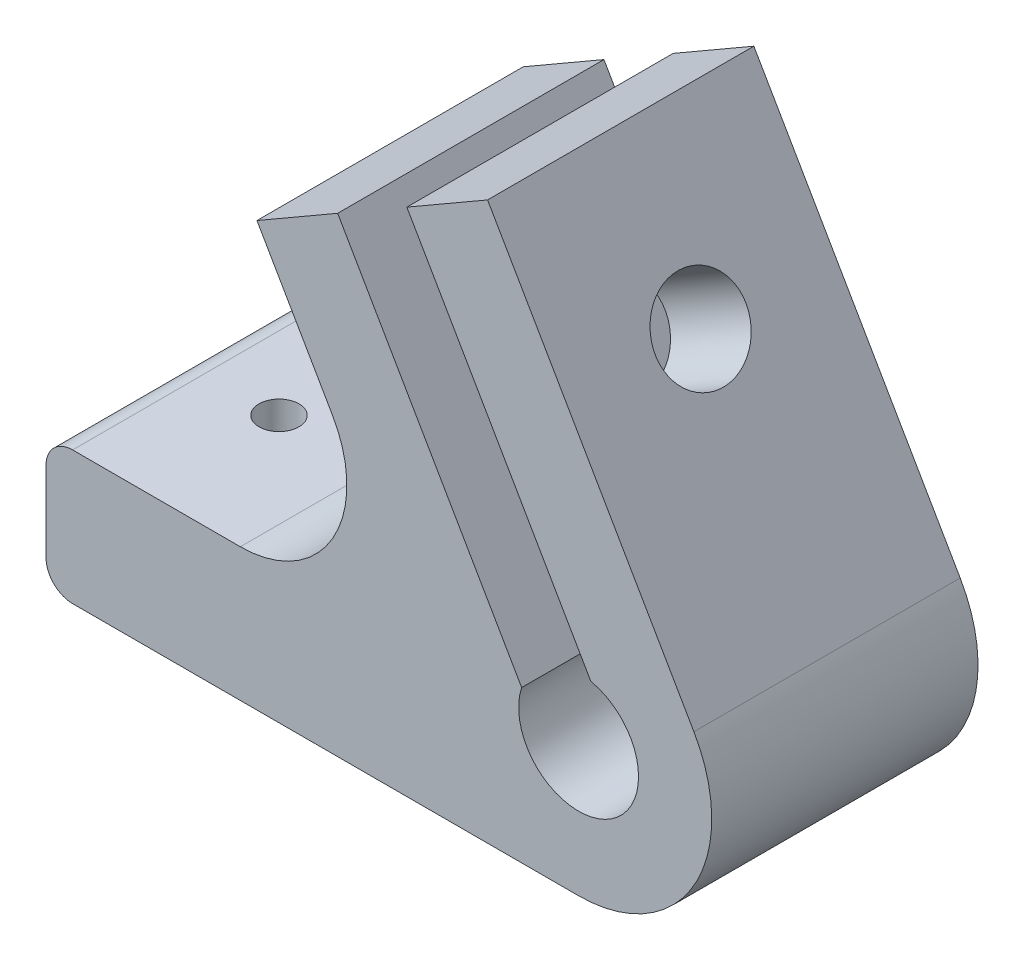
SolidWorks part; units mm, degrees
ref_plane "前视基准面" through (0, 0, 0) normal (0, 0, 1) x (1, 0, 0)
ref_plane "上视基准面" through (0, 0, 0) normal (0, 1, 0) x (1, 0, 0)
ref_plane "右视基准面" through (0, 0, 0) normal (1, 0, 0) x (0, 0, -1)
ref_plane "基准面4" through (0, 0, 10) normal (0, 0, 1) x (1, 0, 0)
sketch "草图1" plane through (0, 0, 10) normal (0, 0, 1) x (1, 0, 0)
  line L0 (904.3301, 2.5) -> (896.5815, 15.921)
  line L1 (896.5815, 15.921) -> (887.9212, 10.921)
  line L2 (887.9212, 10.921) -> (890.7624, 6)
  line L3 (887.2983, 0) -> (880, 0)
  line L4 (880, 0) -> (880, -5)
  line L5 (880, -5) -> (900, -5)
  arc A0 (890.7624, 6) -> (887.2983, 0) centre (887.2983, 4) cw
  arc A1 (900, -5) -> (904.3301, 2.5) centre (900, 0) ccw
extrude "凸台-拉伸1" add sketch "草图1" against normal blind 10
sketch "草图2" plane through (0, 0, 0) normal (0, 0, -1) x (-1, 0, 0)
  line L0 (-890.9523, 12.671) -> (-893.5504, 14.171)
  line L1 (-893.5504, 14.171) -> (-900.4605, 2.2024)
  line L2 (-897.8624, 0.7024) -> (-890.9523, 12.671)
  arc A0 (-900.4605, 2.2024) -> (-897.8624, 0.7024) centre (-900, 0) cw
extrude "切除-拉伸1" cut sketch "草图2" against normal through all
ref_plane "基准面5" through (671.5359, 387.7114, 0) normal (0.866, 0.5, 0) x (-0.5, 0.866, 0)
sketch "草图3" plane through (671.5359, 387.7114, 0) normal (0.866, 0.5, 0) x (-0.5, 0.866, 0)
  line L0 (-437.6448, 6.65) -> (-440.5027, 8.3)
  line L1 (-440.5027, 8.3) -> (-443.3606, 6.65)
  line L2 (-443.3606, 6.65) -> (-443.3606, 3.35)
  line L3 (-443.3606, 3.35) -> (-440.5027, 1.7)
  line L4 (-440.5027, 1.7) -> (-437.6448, 3.35)
  line L5 (-437.6448, 3.35) -> (-437.6448, 6.65)
extrude "切除-拉伸2" cut sketch "草图3" against normal up to next
sketch "草图4" plane through (0, 0, 0) normal (0, 1, 0) x (1, 0, 0)
  line L0 (902.25, 0) -> (900, 0)
  line L1 (900, 0) -> (900, -10)
  line L2 (900, -10) -> (902.25, -10)
  line L3 (902.25, -10) -> (902.25, 0)
  line L4 (900, 0) -> (900, -10) construction
revolve "切除-旋转1" cut sketch "草图4" angle 360 about L4
hole_wizard "Ø3.4 (3.4) 直径孔1" positions "草图6" profile "草图5" hole size "Ø3.4" standard "ANSI Metric"
sketch "草图6" plane through (679.3301, 392.2114, 0) normal (0.866, 0.5, 0) x (0, 0, -1)
  point P0 (-5, -440.5027)
sketch "草图5" plane through (899.5815, 10.7249, 5) normal (0, 0, 1) x (-0.5, 0.866, 0)
  line L0 (0, 0) -> (0, 3.5)
  line L1 (0, 3.5) -> (1.7, 3.5)
  line L2 (1.7, 3.5) -> (1.7, 0)
  line L5 (1.7, 0) -> (0, 0)
  line L11 (0, -6.35) -> (0, 107.95) construction
  dimension "通孔孔直径" = 3.4
  dimension "通孔孔深度" = 3.5
hole_wizard "Ø1.5 (1.5) 直径孔1" positions "草图8" profile "草图7" hole size "Ø1.5" standard "ANSI Metric"
sketch "草图8" plane through (0, 0, 0) normal (0, 1, 0) x (1, 0, 0)
  point P0 (883.75, -5)
sketch "草图7" plane through (883.75, 0, 5) normal (1, 0, 0) x (0, 0, 1)
  line L0 (0, 0) -> (0, 5)
  line L1 (0, 5) -> (0.75, 5)
  line L2 (0.75, 5) -> (0.75, 0)
  line L5 (0.75, 0) -> (0, 0)
  line L11 (0, -6.35) -> (0, 107.95) construction
  dimension "通孔孔直径" = 1.5
  dimension "通孔孔深度" = 5
hole_wizard "Ø3.4 (3.4) 直径孔2" positions "草图10" profile "草图9" hole size "Ø3.4" standard "ANSI Metric"
sketch "草图10" plane through (671.5359, 387.7114, 0) normal (-0.866, -0.5, 0) x (0, 0, 1)
  point P0 (5, -440.5027)
sketch "草图9" plane through (891.7873, 6.2249, 5) normal (0, 0, 1) x (0.5, -0.866, 0)
  line L0 (0, 0) -> (0, 16.2906)
  line L1 (0, 16.2906) -> (1.7, 16.2906)
  line L2 (1.7, 16.2906) -> (1.7, 0)
  line L5 (1.7, 0) -> (0, 0)
  line L11 (0, -6.35) -> (0, 107.95) construction
  dimension "通孔孔直径" = 3.4
  dimension "通孔孔深度" = 16.2906
hole_wizard "Ø1.5 (1.5) 直径孔2" positions "草图12" profile "草图11" hole size "Ø1.5" standard "ANSI Metric"
sketch "草图12" plane through (0, -5, 0) normal (0, -1, 0) x (-1, 0, 0)
  point P0 (-890.25, -5)
sketch "草图11" plane through (890.25, -5, 5) normal (1, 0, 0) x (0, 0, -1)
  line L0 (0, 0) -> (0, 6.3005)
  line L1 (0, 6.3005) -> (0.75, 6.3005)
  line L2 (0.75, 6.3005) -> (0.75, 0)
  line L5 (0.75, 0) -> (0, 0)
  line L11 (0, -6.35) -> (0, 107.95) construction
  dimension "通孔孔直径" = 1.5
  dimension "通孔孔深度" = 6.3005
fillet "圆角1" radius 1 2 edges at (880, -5, 5) (880, 0, 5)
